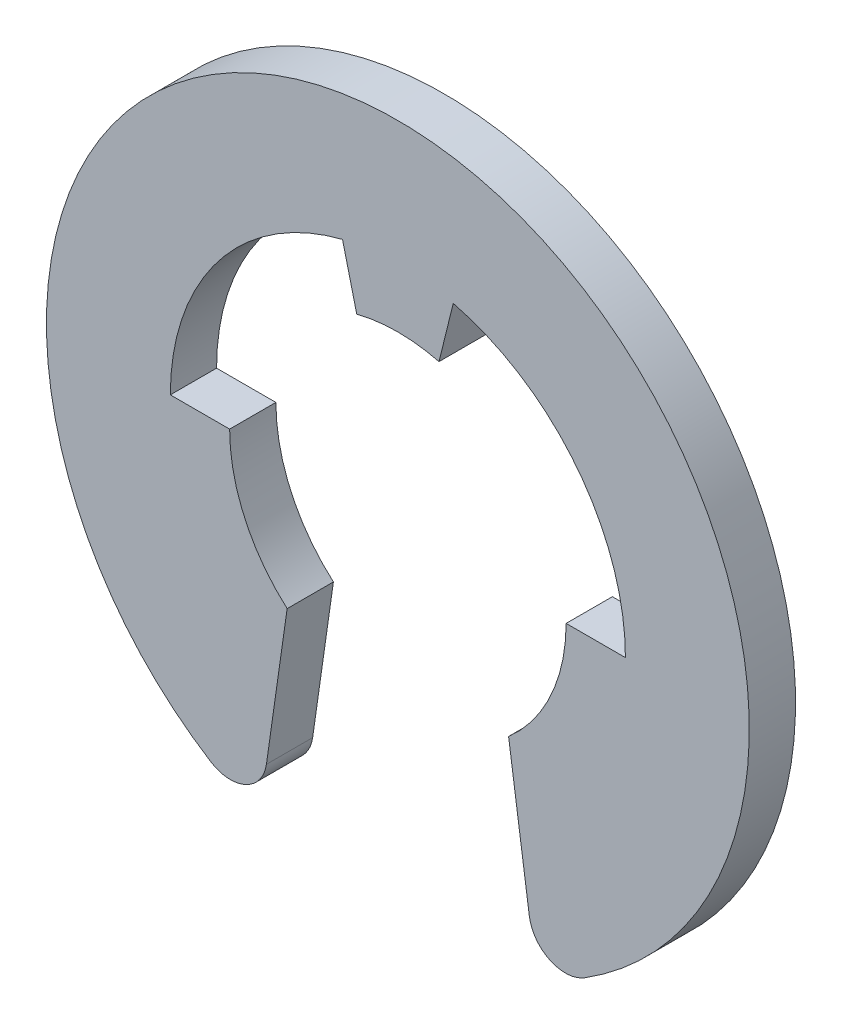
SolidWorks part; units mm, degrees
ref_plane "Front Plane" through (0, 0, 0) normal (0, 0, 1) x (1, 0, 0)
ref_plane "Top Plane" through (0, 0, 0) normal (0, 1, 0) x (1, 0, 0)
ref_plane "Right Plane" through (0, 0, 0) normal (1, 0, 0) x (0, 0, -1)
sketch "Sketch1" plane through (0, 0, 0) normal (0, 0, 1) x (1, 0, 0)
  line L0 (-2.31, 0) -> (-3.1242, 0)
  line L1 (0, 4.825) -> (0, -4.825) construction
  line L2 (-1.52, -1.7395) -> (-1.805, -3.7335)
  line L3 (-0.565, 2.2398) -> (-0.76, 3.0303)
  line L4 (1.52, -1.7395) -> (1.805, -3.7335)
  line L5 (2.31, 0) -> (3.1242, 0)
  line L6 (0.565, 2.2398) -> (0.76, 3.0303)
  arc A0 (-2.31, 0) -> (-1.52, -1.7395) centre (0, 0) ccw
  arc A2 (2.5659, -4.0862) -> (-2.5659, -4.0862) centre (0, 0) ccw
  arc A3 (0.565, 2.2398) -> (-0.565, 2.2398) centre (0, 0) ccw
  arc A4 (-0.76, 3.0303) -> (-3.1242, 0) centre (0, 0) ccw
  arc A5 (2.31, 0) -> (1.52, -1.7395) centre (0, 0) cw
  arc A6 (0.76, 3.0303) -> (3.1242, 0) centre (0, 0) cw
  arc A7 (1.805, -3.7335) -> (2.5659, -4.0862) centre (2.3, -3.6627) ccw
  arc A8 (-1.805, -3.7335) -> (-2.5659, -4.0862) centre (-2.3, -3.6627) cw
  point P18 (1.905, -4.433)
  point P21 (-1.905, -4.433)
  dimension "D1" = 9.65
  dimension "D2" = 3.81
  dimension "D3" = 4.62
  dimension "D7" = 0.5
  dimension "D4" = 3.04
  dimension "D5" = 1.52
  dimension "D6" = 1.13
extrude "Boss-Extrude1" add sketch "Sketch1" along normal mid plane 0.635
